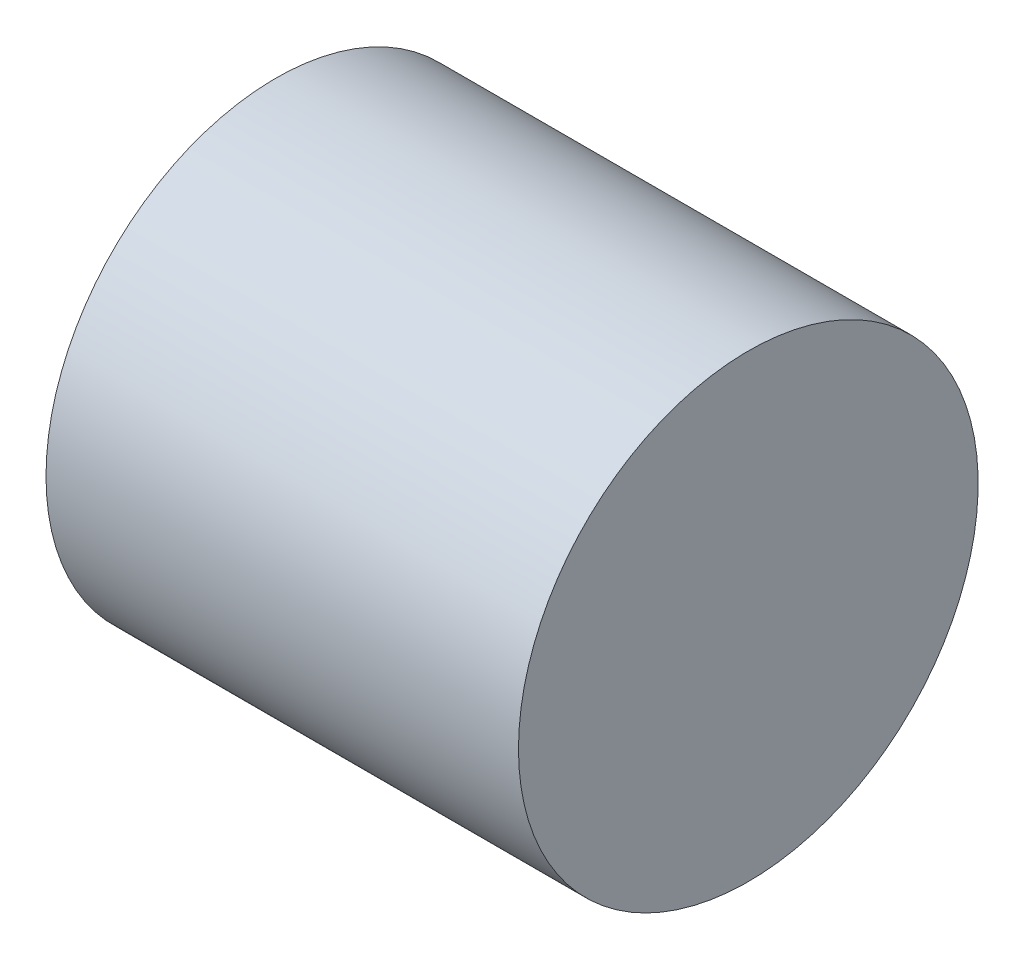
SolidWorks part; units mm, degrees
ref_plane "Front Plane" through (0, 0, 0) normal (0, 0, 1) x (1, 0, 0)
ref_plane "Top Plane" through (0, 0, 0) normal (0, 1, 0) x (1, 0, 0)
ref_plane "Right Plane" through (0, 0, 0) normal (1, 0, 0) x (0, 0, -1)
sketch "Sketch1" plane through (0, 0, 0) normal (0, 0, 1) x (1, 0, 0)
  line L0 (-19.537, 0) -> (23.5185, 0) construction
  line L1 (17.6852, 0) -> (17.6852, 18)
  line L2 (17.6852, 18) -> (-19.3148, 18)
  line L3 (-19.3148, 18) -> (-19.3148, 1)
  line L4 (-19.3148, 1) -> (-17.3148, 1)
  line L5 (-17.3148, 1) -> (-17.3148, 0)
  line L6 (17.6852, 0) -> (-17.3148, 0)
  dimension "D1" = 18
  dimension "D2" = 37
  dimension "D3" = 2
  dimension "D4" = 1
revolve "Revolve1" add sketch "Sketch1" angle 360 about L0
scale "Scale1" scale about centroid uniform scaling yes scale factor 50
